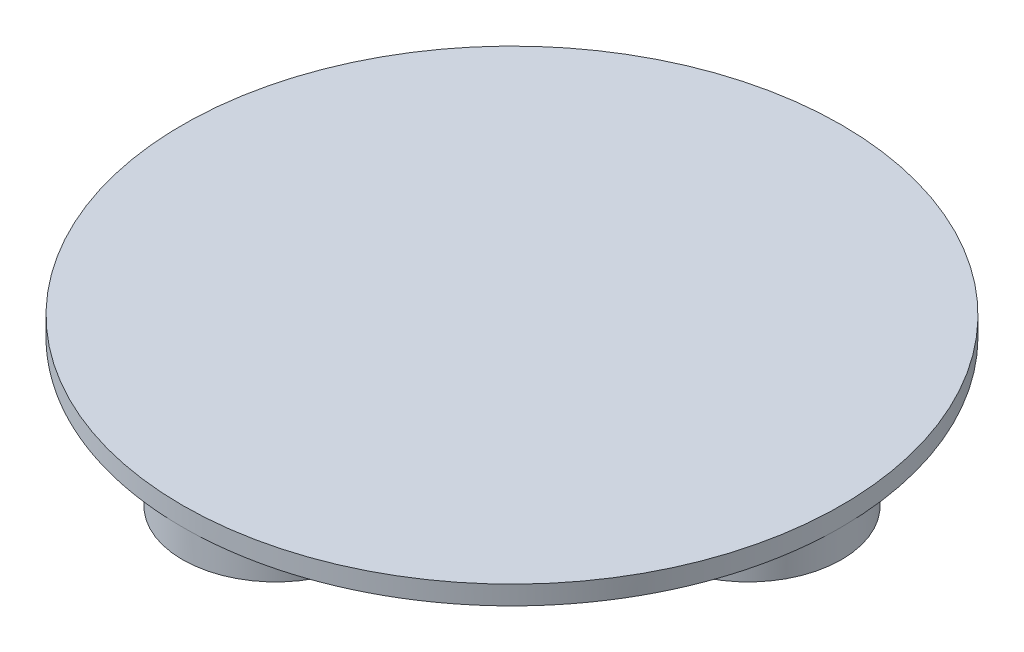
SolidWorks part; units mm, degrees
ref_plane "Front Plane" through (0, 0, 0) normal (0, 0, 1) x (1, 0, 0)
ref_plane "Top Plane" through (0, 0, 0) normal (0, 1, 0) x (1, 0, 0)
ref_plane "Right Plane" through (0, 0, 0) normal (1, 0, 0) x (0, 0, -1)
sketch "Sketch1" plane through (0, 0, 0) normal (0, 1, 0) x (1, 0, 0)
  line L0 (0, 35) -> (0, 25) construction
  circle A0 centre (0, 0) radius 35
extrude "Boss-Extrude1" add sketch "Sketch1" along normal blind 2
sketch "Sketch3" plane through (0, 0, 0) normal (0, -1, 0) x (1, 0, 0)
  line L0 (35, 0) -> (25.1, 0) construction
  circle A0 centre (0, 0) radius 35 construction
  circle A1 centre (25.1, 0) radius 9.9
  circle A2 centre (0, -25.1) radius 9.9
  circle A3 centre (-25.1, 0) radius 9.9
  circle A4 centre (0, 25.1) radius 9.9
  point P15 (0, 0)
  dimension "D1" = 4
extrude "Boss-Extrude2" add sketch "Sketch3" along normal blind 3
